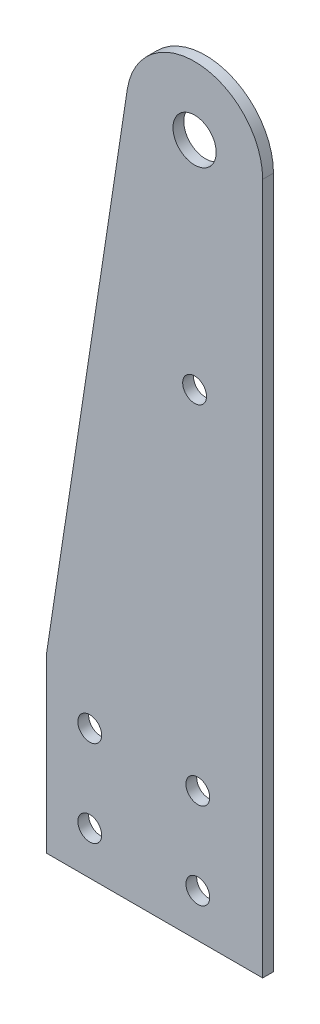
SolidWorks part; units mm, degrees
ref_plane "Front Plane" through (0, 0, 0) normal (0, 0, 1) x (1, 0, 0)
ref_plane "Top Plane" through (0, 0, 0) normal (0, 1, 0) x (1, 0, 0)
ref_plane "Right Plane" through (0, 0, 0) normal (1, 0, 0) x (0, 0, -1)
sketch "Sketch1" plane through (0, 0, 0) normal (0, 0, 1) x (1, 0, 0)
  line L0 (-31.75, -25.4) -> (31.75, -25.4)
  line L2 (31.75, -25.4) -> (31.75, 177.8)
  line L3 (-8.0209, 180.8186) -> (-31.75, 25.4)
  line L5 (-31.75, 25.4) -> (-31.75, -25.4)
  line L6 (-31.75, 25.4) -> (31.75, -25.4) construction
  line L13 (-19.05, -12.7) -> (12.7, -12.7) construction
  line L14 (-19.05, -12.7) -> (-19.05, 12.7) construction
  line L15 (-19.05, 12.7) -> (12.7, 12.7) construction
  line L16 (12.7, -12.7) -> (12.7, 12.7) construction
  line L17 (-19.05, -12.7) -> (12.7, 12.7) construction
  line L18 (-19.05, 12.7) -> (12.7, -12.7) construction
  arc A0 (-8.0209, 180.8186) -> (31.75, 177.8) centre (11.75, 177.8) cw
  circle A1 centre (11.75, 177.8) radius 6.35
  circle A6 centre (-19.05, 12.7) radius 3.5
  circle A7 centre (12.7, 12.7) radius 3.5
  circle A8 centre (12.7, -12.7) radius 3.5
  circle A9 centre (-19.05, -12.7) radius 3.5
  circle A10 centre (11.75, 114.3) radius 3.5
  point P7 (0, 0)
  point P8 (0, 0)
  point P9 (-3.175, 0)
  dimension "D2" = 12.7
  dimension "D6" = 20
  dimension "D5" = 19.05
  dimension "D9" = 7
  dimension "D1" = 50.8
  dimension "D3" = 63.5
  dimension "D4" = 152.4
  dimension "D7" = 25.4
  dimension "D8" = 31.75
  dimension "D10" = 63.5
extrude "Boss-Extrude1" add sketch "Sketch1" along normal blind 3.175
